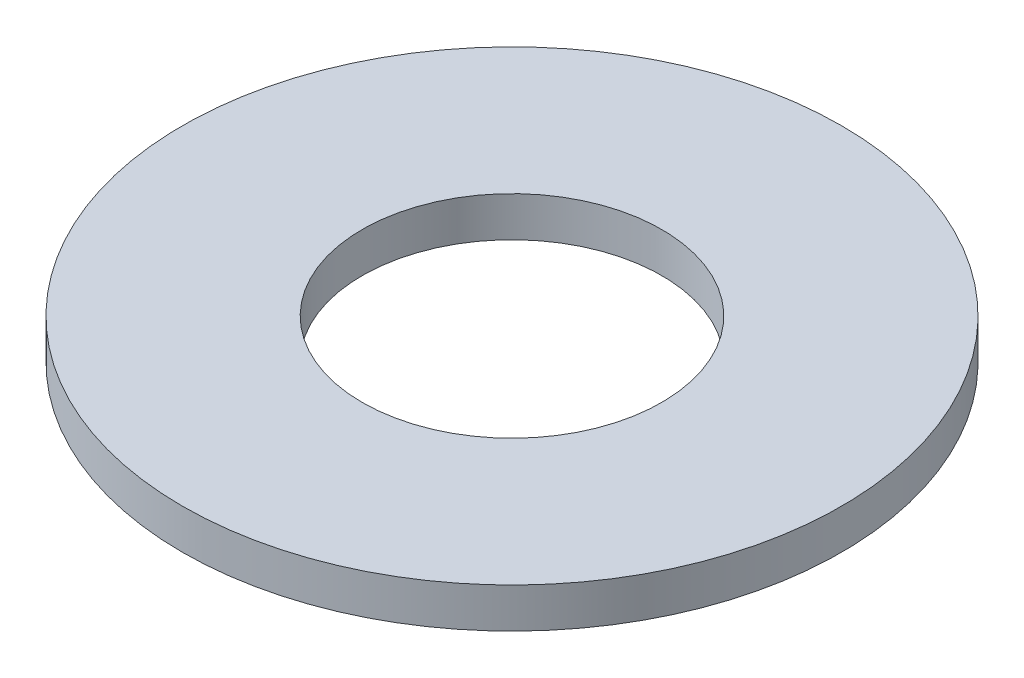
SolidWorks part; units mm, degrees
ref_plane "Front Plane" through (0, 0, 0) normal (0, 0, 1) x (1, 0, 0)
ref_plane "Top Plane" through (0, 0, 0) normal (0, 1, 0) x (1, 0, 0)
ref_plane "Right Plane" through (0, 0, 0) normal (1, 0, 0) x (0, 0, -1)
sketch "Sketch1" plane through (0, 0, 0) normal (0, 1, 0) x (1, 0, 0)
  circle A0 centre (0, 0) radius 82.5
  circle A1 centre (0, 0) radius 37.5
  dimension "D1" = 165
  dimension "D2" = 75
extrude "Boss-Extrude1" add sketch "Sketch1" along normal mid plane 10
